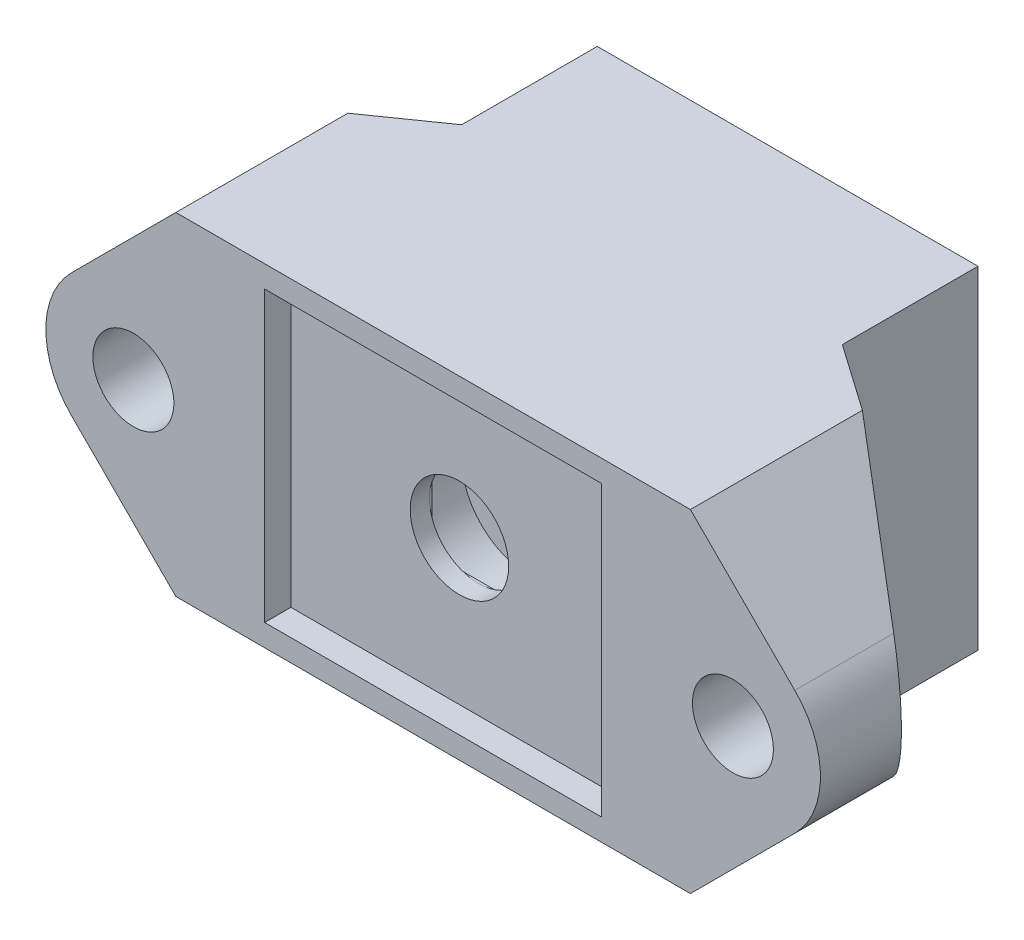
SolidWorks part; units mm, degrees
ref_plane "Front Plane" through (0, 0, 0) normal (0, 0, 1) x (1, 0, 0)
ref_plane "Top Plane" through (0, 0, 0) normal (0, 1, 0) x (1, 0, 0)
ref_plane "Right Plane" through (0, 0, 0) normal (1, 0, 0) x (0, 0, -1)
sketch "Sketch1" plane through (0, 0, 0) normal (0, 0, 1) x (1, 0, 0)
  line L0 (-7.7, -6.6) -> (7.7, 6.6) construction
  line L1 (-8.7, -7.6) -> (8.7, -7.6)
  line L2 (-8.7, -7.6) -> (-8.7, 7.6)
  line L3 (-8.7, 7.6) -> (8.7, 7.6)
  line L4 (8.7, -7.6) -> (8.7, 7.6)
  line L5 (-8.7, 7.6) -> (8.7, -7.6) construction
  line L7 (-7.7, -6.6) -> (7.7, -6.6) construction
  line L8 (-7.7, -6.6) -> (-7.7, 6.6) construction
  line L9 (-7.7, 6.6) -> (7.7, 6.6) construction
  line L10 (7.7, -6.6) -> (7.7, 6.6) construction
  circle A0 centre (0, 0) radius 1.65
  point P11 (0, 0)
  point P12 (0, 0)
  dimension "D1" = 3.3
  dimension "D2" = 1
  dimension "D3" = 1
  dimension "D4" = 15.4
  dimension "D5" = 13.2
extrude "Boss-Extrude1" add sketch "Sketch1" along normal blind 5
sketch "Sketch2" plane through (0, 0, 5) normal (0, 0, 1) x (1, 0, 0)
  line L5 (-8.7, 7.6) -> (8.7, 7.6)
  line L6 (-8.7, 7.6) -> (-8.7, -7.6)
  line L7 (-8.7, -7.6) -> (8.7, -7.6)
  line L8 (7.7, -6.6) -> (7.7, 6.6)
  line L9 (7.7, 6.6) -> (-7.7, 6.6)
  line L10 (-7.7, 6.6) -> (-7.7, -6.6)
  line L11 (-7.7, -6.6) -> (7.7, -6.6)
  line L12 (7.7, -6.6) -> (7.7, 6.6)
  line L13 (7.7, 6.6) -> (-7.7, 6.6)
  line L14 (-7.7, 6.6) -> (-7.7, -6.6)
  line L15 (-7.7, -6.6) -> (7.7, -6.6)
  line L16 (8.7, 7.6) -> (8.7, -7.6)
  dimension "D1" = 1
extrude "Boss-Extrude2" add sketch "Sketch2" along normal blind 1.2
sketch "Sketch3" plane through (0, 0, 5) normal (0, 0, 1) x (1, 0, 0)
  circle A0 centre (0, 0) radius 3.1
  dimension "D1" = 6.2
extrude "Cut-Extrude1" cut sketch "Sketch3" against normal blind 2.2 from offset 1 offset against normal yes
sketch "Sketch4" plane through (0, 0, 5) normal (0, 0, 1) x (1, 0, 0)
  circle A0 centre (0, 0) radius 2.25
  dimension "D1" = 4.5
extrude "Cut-Extrude2" cut sketch "Sketch4" against normal up to surface (1 mm away) up to face at (1.65, 0, 4)
sketch "Sketch6" plane through (0, 0, 4) normal (0, 0, -1) x (-1, 0, 0)
  line L1 (-2.25, -2.25) -> (2.25, -2.25)
  line L2 (-2.25, -2.25) -> (-2.25, 2.25)
  line L3 (-2.25, 2.25) -> (2.25, 2.25)
  line L4 (2.25, -2.25) -> (2.25, 2.25)
  line L5 (-2.25, -2.25) -> (2.25, 2.25) construction
  line L6 (-2.25, 2.25) -> (2.25, -2.25) construction
  circle A1 centre (0, 0) radius 2.25 construction
  point P0 (0, 0)
extrude "Cut-Extrude4" cut sketch "Sketch6" against normal blind 0.12
sketch "Sketch7" plane through (0, 0, 0) normal (0, 0, -1) x (-1, 0, 0)
  line L1 (8.7, -7.6) -> (-8.7, -7.6)
  line L2 (8.7, -7.6) -> (8.7, 7.6)
  line L3 (8.7, 7.6) -> (-8.7, 7.6)
  line L4 (-8.7, -7.6) -> (-8.7, 7.6)
  line L5 (8.7, -7.6) -> (-8.7, 7.6) construction
  line L6 (8.7, 7.6) -> (-8.7, -7.6) construction
  circle A0 centre (0, 0) radius 4.23
  dimension "D1" = 8.46
extrude "Boss-Extrude3" add sketch "Sketch7" along normal blind 10
chamfer "Chamfer1" distance 3 angle 10 1 edges at (-4.23, 0, -10)
sketch "Sketch9" plane through (0, 0, 6.2) normal (0, 0, 1) x (1, 0, 0)
  line L0 (0, 0) -> (0, 9.434) construction
  line L1 (7.7, -6.6) -> (7.7, 6.6) construction
  line L2 (8.7, -7.6) -> (8.7, 7.6) construction
  line L3 (8.7, 7.6) -> (8.7, -7.6)
  line L4 (-8.7, 7.6) -> (-8.7, -7.6)
  line L5 (-16.5284, 2.8284) -> (-11.7569, 7.6)
  line L7 (-11.7569, 7.6) -> (-8.7, 7.6)
  line L8 (-8.7, -7.6) -> (-11.7569, -7.6)
  line L9 (-11.7569, -7.6) -> (-16.5284, -2.8284)
  line L10 (8.7, -7.6) -> (11.7569, -7.6)
  line L11 (11.7569, -7.6) -> (16.5284, -2.8284)
  line L12 (11.7569, 7.6) -> (8.7, 7.6)
  line L13 (16.5284, 2.8284) -> (11.7569, 7.6)
  circle A0 centre (13.7, 0) radius 1.85
  arc A3 (16.5284, -2.8284) -> (16.5284, 2.8284) centre (13.7, 0) ccw
  arc A8 (-16.5284, -2.8284) -> (-16.5284, 2.8284) centre (-13.7, 0) cw
  circle A9 centre (-13.7, 0) radius 1.85
  dimension "D1" = 3.7
  dimension "D2" = 8
  dimension "D3" = 2
  dimension "D4" = 45
extrude "Boss-Extrude5" add sketch "Sketch9" against normal blind 10
sketch "Sketch10" plane through (0, -7.6, 0) normal (0, -1, 0) x (1, 0, 0)
  line L0 (-8.7, -3.8) -> (-19.6072, 3.8373)
  line L5 (0, 0) -> (0, 7.7633) construction
  line L6 (-19.6072, 3.8373) -> (-19.6072, -3.8)
  line L7 (-19.6072, -3.8) -> (-8.7, -3.8)
  line L8 (19.6072, -3.8) -> (8.7, -3.8)
  line L9 (19.6072, 3.8373) -> (19.6072, -3.8)
  line L10 (8.7, -3.8) -> (19.6072, 3.8373)
  dimension "D1" = 35
extrude "Cut-Extrude5" cut sketch "Sketch10" against normal through all
chamfer "Chamfer3" distance 1.4 angle 60 1 edges at (-4.23, 0, 0)
equation "\"D3@Sketch1\"=\"D2@Sketch1\""
